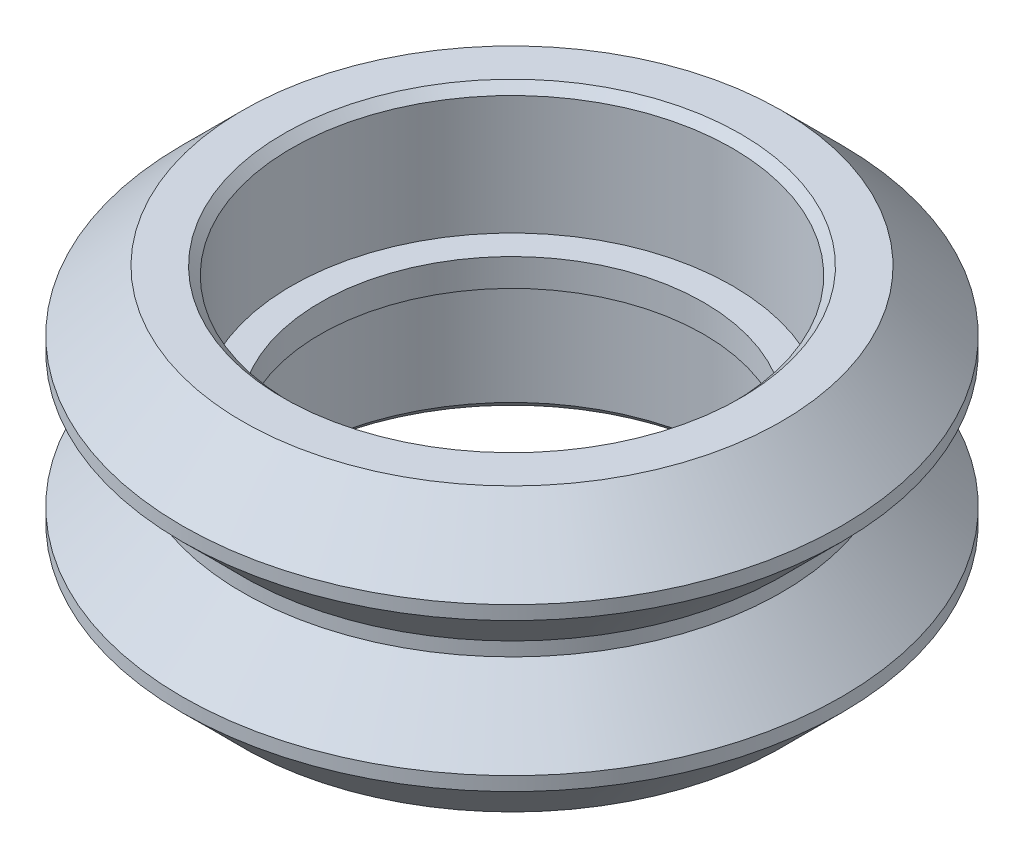
SolidWorks part; units mm, degrees
material "Delrin 2700 NC010, Low Viscosity Acetal Copolymer (SS)"
ref_plane "Plane1" through (0, 0, 0) normal (0, 0, 1) x (1, 0, 0)
ref_plane "Plane2" through (0, 0, 0) normal (0, 1, 0) x (1, 0, 0)
ref_plane "Plane3" through (0, 0, 0) normal (1, 0, 0) x (0, 0, -1)
sketch "Sketch1" plane through (0, 0, 0) normal (0, 0, 1) x (1, 0, 0)
  line L0 (0, 0) -> (0, 10.23) construction
  line L1 (7.987, 9.93) -> (7.987, 5.615)
  line L2 (8.287, 10.23) -> (9.7625, 10.23)
  line L3 (9.7625, 10.23) -> (11.945, 8.0475)
  line L4 (11.945, 8.0475) -> (11.945, 7.5475)
  line L5 (9.7625, 5.365) -> (9.7625, 4.865)
  line L6 (7.987, 5.115) -> (9.7625, 5.115) construction
  line L7 (11.945, 7.5475) -> (9.7625, 5.365)
  line L8 (11.945, 8.0475) -> (12.195, 7.7975) construction
  line L9 (12.195, 7.7975) -> (11.945, 7.5475) construction
  line L10 (7.987, 5.615) -> (6.945, 5.615)
  line L11 (6.945, 5.615) -> (6.945, 4.615)
  line L12 (0, 5.115) -> (7.987, 5.115) construction
  line L13 (8.287, 10.23) -> (7.987, 9.93)
  line L14 (7.987, 4.615) -> (6.945, 4.615)
  line L15 (7.987, 0.3) -> (7.987, 4.615)
  line L16 (8.287, 0) -> (7.987, 0.3)
  line L17 (8.287, 0) -> (9.7625, 0)
  line L18 (9.7625, 0) -> (11.945, 2.1825)
  line L19 (11.945, 2.1825) -> (11.945, 2.6825)
  line L20 (11.945, 2.6825) -> (9.7625, 4.865)
  point P4 (7.987, 10.23)
  point P18 (6.945, 5.115)
  dimension "D1" = 10.23
  dimension "D2" = 45
  dimension "D3" = 0.5
  dimension "D4" = 0.25
  dimension "D5" = 24.39
  dimension "D6" = 1
  dimension "D7" = 15.974
  dimension "D8" = 13.89
revolve "Revolution1" add sketch "Sketch1" angle 360 about L0
ref_plane "Plane4" through (0, 5.115, 0) normal (0, 1, 0) x (1, 0, 0)
